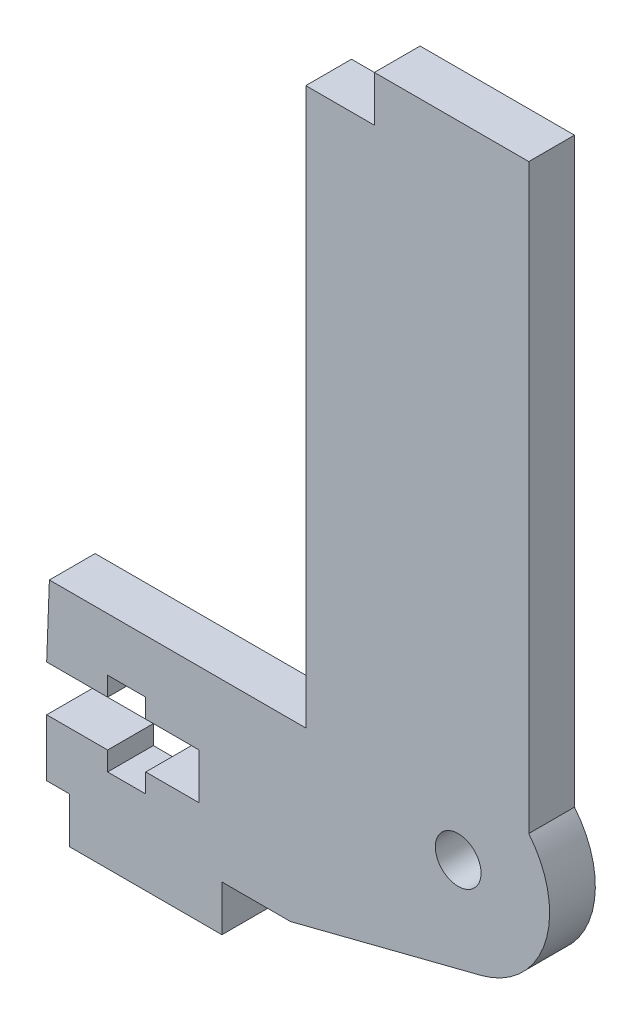
SolidWorks part; units mm, degrees
ref_plane "Front Plane" through (0, 0, 0) normal (0, 0, 1) x (1, 0, 0)
ref_plane "Top Plane" through (0, 0, 0) normal (0, 1, 0) x (1, 0, 0)
ref_plane "Right Plane" through (0, 0, 0) normal (1, 0, 0) x (0, 0, -1)
sketch "Model" plane through (0, 0, 0) normal (0, 0, 1) x (1, 0, 0)
  line L0 (67.7457, 17.4873) -> (67.7457, 21.2373)
  line L1 (69.2457, 17.4873) -> (69.2457, 14.4873)
  line L2 (79.2457, 14.4873) -> (79.2457, 17.4873)
  line L3 (71.7457, 21.2373) -> (67.7457, 21.2373)
  line L4 (74.2457, 21.2373) -> (77.7457, 21.2373)
  line L5 (67.7457, 24.2373) -> (71.7457, 24.2373)
  line L6 (74.2457, 24.2373) -> (77.7457, 24.2373)
  line L7 (77.7457, 21.2373) -> (77.7457, 24.2373)
  line L8 (71.7457, 19.9873) -> (71.7457, 21.2373)
  line L9 (71.7457, 24.2373) -> (71.7457, 25.4873)
  line L10 (74.2457, 25.4873) -> (74.2457, 24.2373)
  line L11 (74.2457, 21.2373) -> (74.2457, 19.9873)
  line L12 (67.7457, 17.4873) -> (69.2457, 17.4873)
  line L14 (68.9957, 28.9873) -> (84.7456, 28.9873)
  line L35 (89.2456, 65.4873) -> (89.2456, 68.4873)
  line L36 (89.2456, 68.4873) -> (99.3761, 68.4873)
  line L37 (99.3761, 68.4873) -> (99.3761, 65.4875)
  line L39 (99.3761, 65.4875) -> (99.3761, 30.303)
  line L40 (71.7457, 19.9873) -> (74.2457, 19.9873)
  line L41 (71.7457, 25.4873) -> (74.2457, 25.4873)
  line L42 (79.2457, 17.4873) -> (83.7457, 17.4873)
  line L43 (83.7457, 17.4873) -> (96.2296, 20.6737)
  line L44 (69.2457, 14.4873) -> (79.2457, 14.4873)
  line L47 (67.9243, 28.9873) -> (67.7457, 24.2373)
  line L48 (89.2456, 65.4873) -> (84.7456, 65.4873)
  line L49 (84.7456, 65.4873) -> (84.7456, 28.9873)
  line L50 (68.9957, 28.9873) -> (67.9243, 28.9873)
  circle A0 centre (94.7457, 26.4873) radius 1.5
  arc A1 (96.2296, 20.6737) -> (99.3761, 30.303) centre (94.7457, 26.4873) ccw
extrude "Boss-Extrude1" add sketch "Model" along normal blind 3
